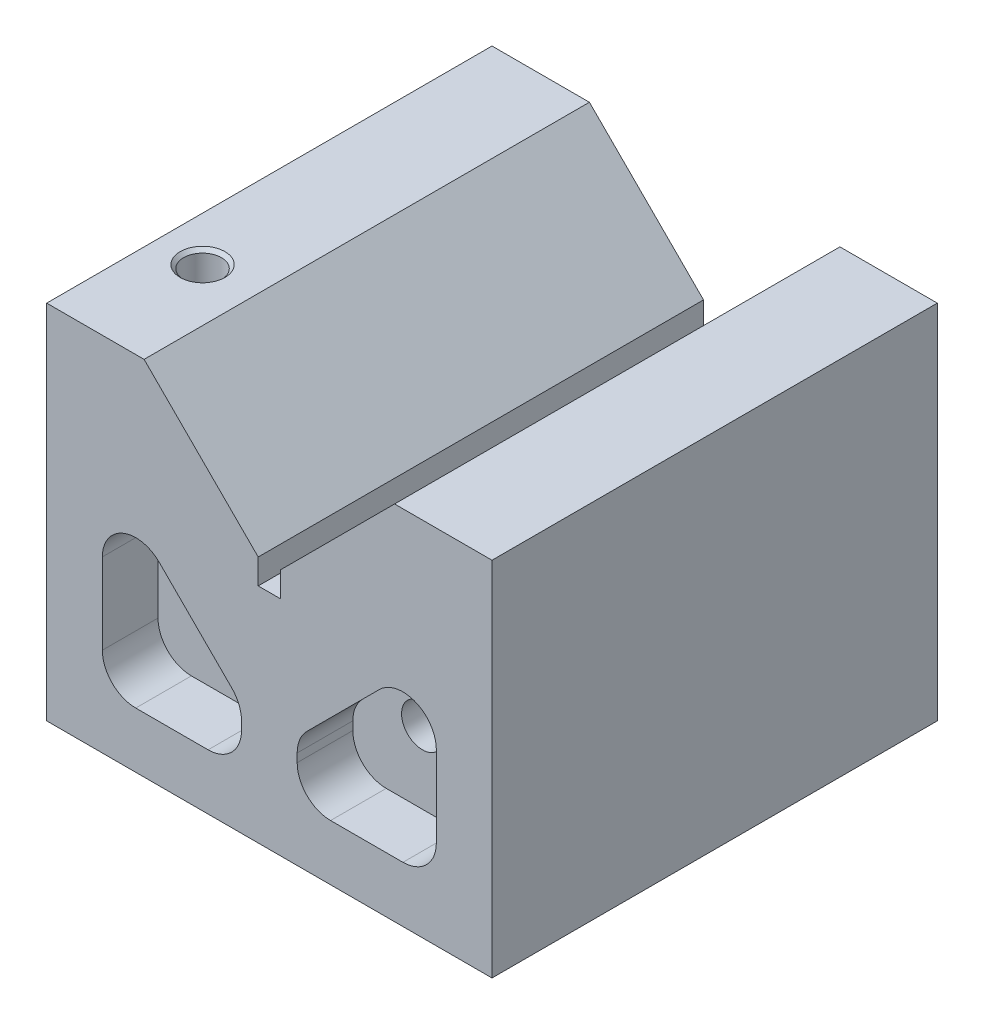
SolidWorks part; units mm, degrees
ref_plane "Ön Düzlem" through (0, 0, 0) normal (0, 0, 1) x (1, 0, 0)
ref_plane "Üst Düzlem" through (0, 0, 0) normal (0, 1, 0) x (1, 0, 0)
ref_plane "Sağ Düzlem" through (0, 0, 0) normal (1, 0, 0) x (0, 0, -1)
sketch "Çizim1" plane through (0, 0, 0) normal (0, 0, 1) x (1, 0, 0)
  line L0 (0, 0) -> (0, 38.3621) construction
  line L1 (2, 0) -> (-2, 0)
  line L2 (-2, 0) -> (-2, 4.5)
  line L3 (-2, 4.5) -> (-22.5, 25)
  line L4 (-22.5, 25) -> (-40, 25)
  line L5 (-40, 25) -> (-40, -40)
  line L6 (-40, -40) -> (40, -40)
  line L7 (0, 0) -> (0, -40) construction
  line L8 (40, 25) -> (40, -40)
  line L9 (22.5, 25) -> (40, 25)
  line L10 (2, 4.5) -> (22.5, 25)
  line L11 (2, 0) -> (2, 4.5)
  point P8 (0, -40.8507)
  point P15 (-101.1677, 1.0336)
  dimension "D1" = 22.5
  dimension "D2" = 2
  dimension "D3" = 25
  dimension "D4" = 65
  dimension "D6" = 38
  dimension "D7" = 135
extrude "Yükseklik-Ekstrüzyon1" add sketch "Çizim1" along normal mid plane 80
sketch "Çizim2" plane through (0, 0, 40) normal (0, 0, 1) x (1, 0, 0)
  line L0 (0, 0) -> (0, -40) construction
  line L1 (-40, -40) -> (40, -40) construction
  line L2 (-40, 25) -> (-40, -40) construction
  line L3 (30, -9.4853) -> (30, -24)
  line L4 (-24, -30) -> (-11, -30)
  line L5 (-5, -24) -> (-5, -22.4853)
  line L6 (-6.7574, -18.2426) -> (-19.7574, -5.2426)
  line L7 (-30, -9.4853) -> (-30, -24)
  line L8 (24, -30) -> (11, -30)
  line L9 (5, -24) -> (5, -22.4853)
  line L10 (0, 0) -> (0, 19.4127) construction
  line L11 (6.7574, -18.2426) -> (19.7574, -5.2426)
  circle A0 centre (-17.5, -17) radius 3.75
  circle A1 centre (17.5, -17) radius 3.75
  arc A2 (-5, -22.4853) -> (-6.7574, -18.2426) centre (-11, -22.4853) ccw
  arc A3 (-5, -24) -> (-11, -30) centre (-11, -24) cw
  arc A4 (-30, -24) -> (-24, -30) centre (-24, -24) ccw
  arc A5 (-30, -9.4853) -> (-19.7574, -5.2426) centre (-24, -9.4853) cw
  arc A6 (30, -24) -> (24, -30) centre (24, -24) cw
  arc A7 (5, -24) -> (11, -30) centre (11, -24) ccw
  arc A8 (5, -22.4853) -> (6.7574, -18.2426) centre (11, -22.4853) cw
  arc A9 (30, -9.4853) -> (19.7574, -5.2426) centre (24, -9.4853) ccw
  point P24 (-30, 5)
  dimension "D1" = 7.5
  dimension "D2" = 7.5
  dimension "D11" = 6
  dimension "D3" = 35
  dimension "D4" = 23
  dimension "D5" = 22.5
  dimension "D6" = 5
  dimension "D7" = 25
  dimension "D8" = 13
  dimension "D9" = 45
  dimension "D10" = 35
extrude "Kes-Ekstrüzyon1" cut sketch "Çizim2" against normal blind 10
mirror "Aynalama1" about plane through (0, 0, 0) normal (0, 0, 1) of "Kes-Ekstrüzyon1"
sketch "Çizim3" plane through (0, 0, 40) normal (0, 0, 1) x (1, 0, 0)
  circle A0 centre (-17.5, -17) radius 3.75
  circle A1 centre (17.5, -17) radius 3.75
  dimension "D1" = 7.5
  dimension "D2" = 7.5
extrude "Kes-Ekstrüzyon2" cut sketch "Çizim3" against normal through all
sketch "Çizim4" plane through (0, 25, 0) normal (0, 1, 0) x (1, 0, 0)
  line L0 (-40, -40) -> (-32, -40) construction
  line L1 (-22.5, -40) -> (-40, -40) construction
  line L2 (-32, -40) -> (-32, -20) construction
  dimension "D1" = 8
  dimension "D2" = 20
hole_wizard "M8 Dişli Delik1" positions "Çizim5" profile "Çizim6" tap size "M8" standard "ISO"
sketch "Çizim5" plane through (0, 25, 0) normal (0, 1, 0) x (1, 0, 0)
  point P0 (-32, -20)
cosmetic thread "Delik Dişi1" parameters "D2"=8
sketch "Çizim6" plane through (-32, 25, 20) normal (1, 0, 0) x (0, 0, 1)
  line L0 (0, 0) -> (0, 20.0429)
  line L1 (0, 20.0429) -> (3.4, 18)
  line L2 (3.4, 18) -> (3.4, 0.625)
  line L3 (3.4, 0.625) -> (4.025, 0)
  line L5 (4.025, 0) -> (0, 0)
  line L6 (-3.4, 0.625) -> (-4.025, 0) construction
  line L10 (0, 20.0429) -> (-3.4, 18) construction
  line L11 (0, -6.35) -> (0, 107.95) construction
  dimension "Tap Drill Dia." = 6.8
  dimension "Tap Drill Depth" = 18
  dimension "Near C'Sink Dia." = 8.05
  dimension "Near C'Sink Angle" = 90
  dimension "Drill Angle" = 118
